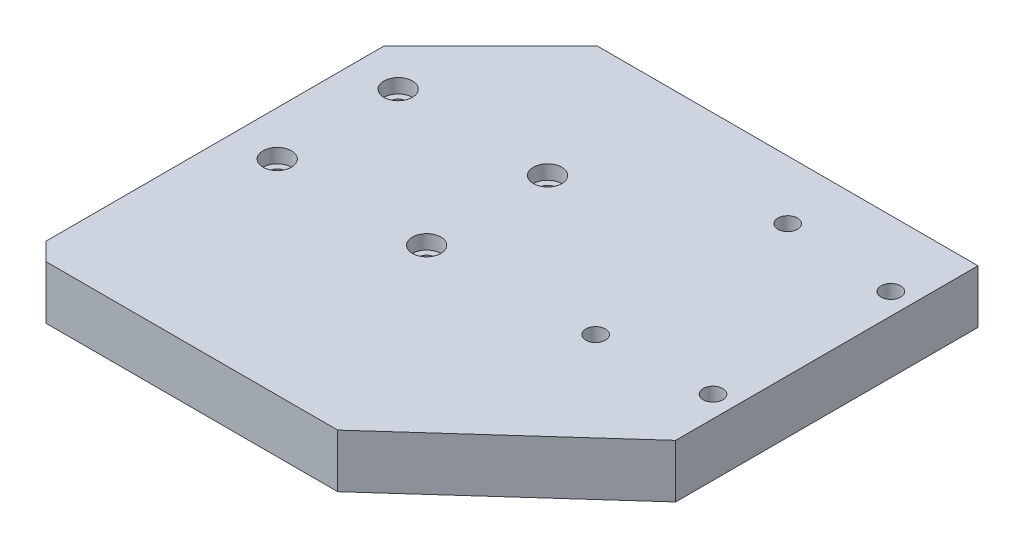
SolidWorks part; units mm, degrees
ref_plane "Front" through (0, 0, 0) normal (0, 0, 1) x (1, 0, 0)
ref_plane "Top" through (0, 0, 0) normal (0, 1, 0) x (1, 0, 0)
ref_plane "Right" through (0, 0, 0) normal (1, 0, 0) x (0, 0, -1)
sketch "Sketch1" plane through (0, 0, 0) normal (0, 1, 0) x (1, 0, 0)
  line L0 (0, 100) -> (30, 130)
  line L1 (5, 0) -> (87, 0)
  line L2 (0, 5) -> (0, 100)
  line L3 (30, 130) -> (137, 130)
  line L4 (137, 45) -> (137, 120)
  line L5 (137, 45) -> (87, 0)
  line L6 (137, 130) -> (137, 120)
  line L7 (0, 5) -> (5, 0)
  dimension "D1" = 130
  dimension "D2" = 5
  dimension "D3" = 5
  dimension "D4" = 137
  dimension "D5" = 45
  dimension "D6" = 30
  dimension "D7" = 30
  dimension "D8" = 0
  dimension "D10" = 50
extrude "Boss-Extrude1" add sketch "Sketch1" along normal blind 15
hole_wizard "M5 Clearance Hole1" positions "Sketch5" profile "Sketch4" hole size "M5" standard "JIS" end condition through all
sketch "Sketch5" plane through (0, 15, 0) normal (0, 1, 0) x (-1, 0, 0)
  line L0 (0, -100) -> (0, -5) construction
  line L1 (-5, 0) -> (-87, 0) construction
  point P0 (-100, -59.5)
  point P10 (-100, -113.5)
  dimension "D1" = 100
  dimension "D2" = 59.5
  dimension "D3" = 2
sketch "Sketch4" plane through (100, 15, -59.5) normal (1, 0, 0) x (0, 0, 1)
  line L0 (0, 0) -> (0, 15)
  line L1 (0, 15) -> (2.75, 15)
  line L2 (2.75, 15) -> (2.75, 0)
  line L5 (2.75, 0) -> (0, 0)
  line L11 (0, -6.35) -> (0, 107.95) construction
  dimension "通し穴の直径" = 5.5
  dimension "通し穴の深さ" = 15
hole_wizard "M5 Clearance Hole2" positions "Sketch7" profile "Sketch6" hole size "M5" standard "JIS" end condition through all
sketch "Sketch7" plane through (0, 15, 0) normal (0, 1, 0) x (-1, 0, 0)
  line L0 (0, -100) -> (0, -5) construction
  line L1 (-5, 0) -> (-87, 0) construction
  point P0 (-131, -111.5)
  point P1 (-131, -61.5)
  dimension "D1" = 131
  dimension "D2" = 61.5
  dimension "D3" = 50
sketch "Sketch6" plane through (131, 15, -111.5) normal (1, 0, 0) x (0, 0, 1)
  line L0 (0, 0) -> (0, 15)
  line L1 (0, 15) -> (2.75, 15)
  line L2 (2.75, 15) -> (2.75, 0)
  line L5 (2.75, 0) -> (0, 0)
  line L11 (0, -6.35) -> (0, 107.95) construction
  dimension "通し穴の直径" = 5.5
  dimension "通し穴の深さ" = 15
hole_wizard "CBORE for M4 Socket Head Cap Screw1" positions "Sketch9" profile "Sketch8" counterbore size "M4" standard "JIS" end condition through all
sketch "Sketch9" plane through (0, 15, 0) normal (0, 1, 0) x (-1, 0, 0)
  line L0 (-5, 0) -> (-87, 0) construction
  line L1 (0, -100) -> (0, -5) construction
  point P0 (-12.5, -91.5)
  point P1 (-12.5, -57.5)
  point P3 (-54.5, -57.5)
  point P5 (-54.5, -91.5)
  dimension "D1" = 57.5
  dimension "D2" = 12.5
  dimension "D3" = 42
  dimension "D4" = 34
sketch "Sketch8" plane through (12.5, 15, -91.5) normal (1, 0, 0) x (0, 0, 1)
  line L0 (0, 0) -> (0, 15)
  line L1 (0, 15) -> (2.25, 15)
  line L3 (2.25, 15) -> (2.25, 4)
  line L4 (2.25, 4) -> (4, 4)
  line L5 (4, 4) -> (4, 0)
  line L7 (4, 0) -> (0, 0)
  line L11 (0, -6.35) -> (0, 107.95) construction
  dimension "通し穴の直径" = 4.5
  dimension "通し穴の深さ" = 15
  dimension "座ぐり穴の直径" = 8
  dimension "座ぐり穴の深さ" = 4
hole_wizard "CBORE for M5 Socket Head Cap Screw1" [suppressed] positions "Sketch11" profile "Sketch10" counterbore size "M5" standard "JIS"
sketch "Sketch11" plane through (0, 0, 0) normal (0, -1, 0) x (1, 0, 0)
  line L0 (0, -100) -> (0, -5) construction
  line L1 (5, 0) -> (87, 0) construction
  point P0 (27.5, -102.5)
  point P1 (102.5, -102.5)
  dimension "D1" = 27.5
  dimension "D2" = 75
  dimension "D3" = 102.5
sketch "Sketch10" plane through (27.5, 0, -102.5) normal (1, 0, 0) x (0, 0, -1)
  line L0 (0, 0) -> (0, 15)
  line L1 (0, 15) -> (2.75, 15)
  line L3 (2.75, 15) -> (2.75, 5)
  line L4 (2.75, 5) -> (5, 5)
  line L5 (5, 5) -> (5, 0)
  line L7 (5, 0) -> (0, 0)
  line L11 (0, -6.35) -> (0, 107.95) construction
  dimension "通し穴の直径" = 5.5
  dimension "通し穴の深さ" = 15
  dimension "座ぐり穴の直径" = 10
  dimension "座ぐり穴の深さ" = 5
hole_wizard "CBORE for M5 Socket Head Cap Screw2" [suppressed] positions "Sketch13" profile "Sketch12" counterbore size "M5" standard "JIS"
sketch "Sketch13" plane through (0, 0, 0) normal (0, -1, 0) x (1, 0, 0)
  line L1 (5, 0) -> (87, 0) construction
  line L2 (0, -100) -> (0, -5) construction
  point P0 (82, -35)
  point P1 (82, -78)
  dimension "D1" = 35
  dimension "D2" = 43
  dimension "D3" = 82
sketch "Sketch12" plane through (82, 0, -35) normal (1, 0, 0) x (0, 0, -1)
  line L0 (0, 0) -> (0, 15)
  line L1 (0, 15) -> (2.75, 15)
  line L3 (2.75, 15) -> (2.75, 5)
  line L4 (2.75, 5) -> (5, 5)
  line L5 (5, 5) -> (5, 0)
  line L7 (5, 0) -> (0, 0)
  line L11 (0, -6.35) -> (0, 107.95) construction
  dimension "通し穴の直径" = 5.5
  dimension "通し穴の深さ" = 15
  dimension "座ぐり穴の直径" = 10
  dimension "座ぐり穴の深さ" = 5
sketch "Sketch14" plane through (0, 0, 0) normal (0, 1, 0) x (1, 0, 0)
  line L0 (54, 74.5) -> (55, 74.5) construction
  line L1 (54, 76.5) -> (55, 76.5)
  line L2 (54, 72.5) -> (55, 72.5)
  circle A0 centre (12.5, 74.5) radius 2
  arc A1 (54, 76.5) -> (54, 72.5) centre (54, 74.5) ccw
  arc A2 (55, 72.5) -> (55, 76.5) centre (55, 74.5) ccw
  point P2 (54.5, 74.5)
  dimension "D3" = 4
  dimension "D1" = 74.5
  dimension "D2" = 12.5
  dimension "D4" = 42
  dimension "D5" = 4
  dimension "D6" = 1
extrude "Cut-Extrude1" [suppressed] cut sketch "Sketch14" along normal through all
sketch "Эскиз1" plane through (0, 0, 0) normal (-1, 0, 0) x (0, 0, 1)
  line L0 (-5, 15) -> (-5, 0) construction
  line L1 (-100, 0) -> (-5, 0) construction
  point P0 (-50, 7.5)
  point P1 (-20, 7.5)
  dimension "D1" = 30
  dimension "D2" = 15
  dimension "D3" = 7.5
hole_wizard "Отверстие обработанное метчиком M51" positions "Эскиз1" profile "Эскиз2" tap size "M5" standard "ISO"
sketch "Эскиз2" plane through (0, 7.5, -50) normal (0, 1, 0) x (0, 0, 1)
  line L0 (0, 0) -> (0, 15.2618)
  line L1 (0, 15.2618) -> (2.1, 14)
  line L2 (2.1, 14) -> (2.1, 0)
  line L5 (2.1, 0) -> (0, 0)
  line L10 (0, 15.2618) -> (-2.1, 14) construction
  line L11 (0, -6.35) -> (0, 107.95) construction
  dimension "Диаметр сверла" = 4.2
  dimension "Глубина сверла" = 14
  dimension "Угол заточки сверла" = 118
cosmetic thread "Отверстие резьбы5" parameters "D1"=10, "D2"=5
cosmetic thread "Отверстие резьбы6" parameters "D1"=10, "D2"=5
